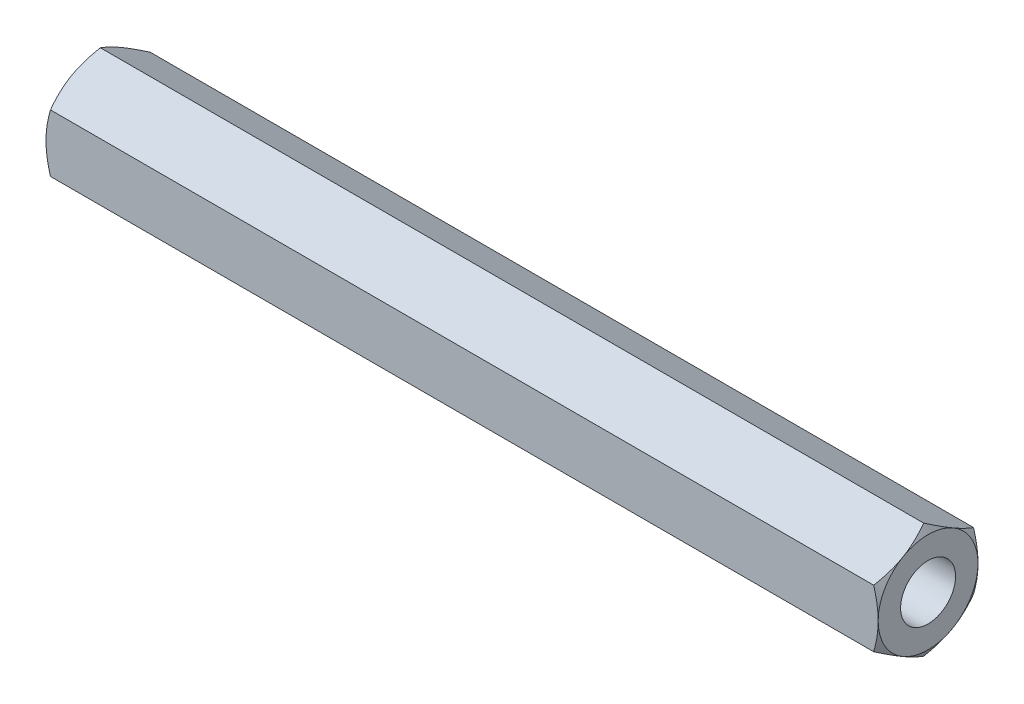
SolidWorks part; units mm, degrees
material "General Structural Steel"
ref_plane "Front Plane" through (0, 0, 0) normal (0, 0, 1) x (1, 0, 0)
ref_plane "Top Plane" through (0, 0, 0) normal (0, 1, 0) x (1, 0, 0)
ref_plane "Right Plane" through (0, 0, 0) normal (1, 0, 0) x (0, 0, -1)
sketch "Sketch1" plane through (0, 0, 0) normal (1, 0, 0) x (0, 0, -1)
  line L3 (0, -3.4641) -> (3, -1.7321)
  line L4 (3, -1.7321) -> (3, 1.7321)
  line L5 (3, 1.7321) -> (0, 3.4641)
  line L6 (0, 3.4641) -> (-3, 1.7321)
  line L7 (-3, 1.7321) -> (-3, -1.7321)
  line L8 (-3, -1.7321) -> (0, -3.4641)
  circle A0 centre (0, 0) radius 3 construction
  dimension "B" = 6
  dimension "C" = 6.9282
extrude "Boss-Extrude1" add sketch "Sketch1" along normal blind 50
sketch "Sketch2" plane through (0, 0, 0) normal (0, 0, 1) x (1, 0, 0)
  line L0 (0, 3.4641) -> (0.2679, 3.4641)
  line L1 (0, 0) -> (50, 0) construction
  line L2 (50, 1.7321) -> (50, -1.7321) construction
  line L3 (0, 3.4641) -> (0, 3)
  line L4 (50, 3.4641) -> (50, 1.7321) construction
  line L5 (50, 3.4641) -> (0, 3.4641) construction
  line L6 (50, 3.4641) -> (0, 3.4641) construction
  line L8 (0.2679, 3.4641) -> (0, 3)
  line L9 (49.7321, 3.4641) -> (50, 3)
  line L15 (50, 3.4641) -> (50, 3)
  line L16 (50, 3.4641) -> (49.7321, 3.4641)
  dimension "D1" = 30
revolve "Cut-Revolve1" cut sketch "Sketch2" angle 360 about L1
hole_wizard "Tapped Hole1" [suppressed] positions "Sketch4" profile "Sketch3" tap size "M3x0.5" standard "JIS"
sketch "Sketch4" [suppressed] plane through (0, 0, 0) normal (-1, 0, 0) x (0, 0, 1)
  point P0 (0, 0)
sketch "Sketch3" [suppressed] plane through (0, 0, 0) normal (0, 1, 0) x (0, 0, 1)
  line L0 (0, 9.2511) -> (0, 0)
  line L1 (0, 9.2511) -> (1.25, 8.5)
  line L2 (1.25, 8.5) -> (1.25, 0)
  line L3 (1.5, 0) -> (1.5, 8.5) construction
  line L5 (1.25, 0) -> (0, 0)
  line L10 (0, 9.2511) -> (-1.25, 8.5) construction
  line L11 (0, 0) -> (0, 9.2511) construction
  dimension "Tap Drill Dia." = 2.5
  dimension "Tap Drill Depth" = 8.5
  dimension "Drill Angle" = 118
  dimension "M" = 4
cosmetic thread "Hole Thread1" [suppressed] parameters "Mx2"=6, "M"=4
hole_wizard "Tapped Hole2" [suppressed] positions "Sketch6" profile "Sketch5" tap size "M3x0.5" standard "JIS"
sketch "Sketch6" [suppressed] plane through (24, 0, 0) normal (1, 0, 0) x (0, 0, -1)
  point P0 (0, 0)
sketch "Sketch5" [suppressed] plane through (24, 0, 0) normal (0, 1, 0) x (0, 0, -1)
  line L0 (0, 0) -> (0, 9.2511)
  line L1 (0, 9.2511) -> (1.25, 8.5)
  line L2 (1.25, 8.5) -> (1.25, 0)
  line L5 (1.25, 0) -> (0, 0)
  line L10 (0, 9.2511) -> (-1.25, 8.5) construction
  line L11 (0, 0) -> (0, 9.2511) construction
  dimension "Tap Drill Dia." = 2.5
  dimension "Tap Drill Depth" = 8.5
  dimension "Drill Angle" = 118
cosmetic thread "Hole Thread2" [suppressed] parameters "Mx2"=6, "M"=4
hole_wizard "Tapped Hole3" [suppressed] positions "Sketch8" profile "Sketch7" tap size "M3x0.5" standard "JIS"
sketch "Sketch8" [suppressed] plane through (0, 0, 0) normal (-1, 0, 0) x (0, 0, 1)
  point P0 (0, 0)
sketch "Sketch7" [suppressed] plane through (0, 0, 0) normal (0, 1, 0) x (0, 0, 1)
  line L0 (0, 0) -> (0, 10)
  line L1 (0, 10) -> (1.25, 10)
  line L2 (1.25, 10) -> (1.25, 0)
  line L5 (1.25, 0) -> (0, 0)
  line L11 (0, 0) -> (0, 10) construction
  dimension "Thru Tap Drill Dia." = 2.5
  dimension "Thru Tap Drill Depth" = 10
cosmetic thread "Hole Thread3" [suppressed] parameters "M"=4
sketch "Sketch21" plane through (0, 0, 0) normal (0, 0, 1) x (1, 0, 0)
  line L0 (0, 0) -> (50, 0)
  line L1 (0, 0) -> (50, 0) construction
  line L2 (0, 0) -> (0, 3)
  line L3 (0, 3) -> (50, 3)
  line L4 (50, 0) -> (50, 3)
revolve "Revolve1" add sketch "Sketch21" angle 360 about L1
hole_wizard "Tapped Hole4" positions "Sketch10" profile "Sketch9" tap size "M4x0.7" standard "JIS"
sketch "Sketch10" plane through (0, -0.1187, 0.0051) normal (1, 0, 0) x (0, 0, -1)
  point P0 (0.0051, 0.1187)
sketch "Sketch9" plane through (0, 0, 0) normal (0, 1, 0) x (0, 0, 1)
  line L0 (0, 0) -> (0, 12.4914)
  line L1 (0, 12.4914) -> (1.65, 11.5)
  line L2 (1.65, 11.5) -> (1.65, 0)
  line L3 (2, 0) -> (2, 11.5) construction
  line L5 (1.65, 0) -> (0, 0)
  line L10 (0, 12.4914) -> (-1.65, 11.5) construction
  line L11 (0, 0) -> (0, 12.4914) construction
  dimension "Tap Drill Dia." = 3.3
  dimension "Tap Drill Depth" = 11.5
  dimension "Drill Angle" = 118
  dimension "M" = 4
cosmetic thread "Hole Thread4" parameters "Mx2"=8, "M"=4
hole_wizard "Tapped Hole5" positions "Sketch12" profile "Sketch11" tap size "M4x0.7" standard "JIS"
sketch "Sketch12" plane through (50, 0.8438, 0.0751) normal (1, 0, 0) x (0, 0, -1)
  point P0 (0.0751, -0.8438)
sketch "Sketch11" plane through (50, 0, 0) normal (0, 1, 0) x (0, 0, -1)
  line L0 (0, 12.4914) -> (0, 0)
  line L1 (0, 12.4914) -> (1.65, 11.5)
  line L2 (1.65, 11.5) -> (1.65, 0)
  line L3 (2, 11.5) -> (2, 0) construction
  line L5 (1.65, 0) -> (0, 0)
  line L10 (0, 12.4914) -> (-1.65, 11.5) construction
  line L11 (0, 0) -> (0, 12.4914) construction
  dimension "Tap Drill Dia." = 3.3
  dimension "Tap Drill Depth" = 11.5
  dimension "Drill Angle" = 118
  dimension "N" = 4
cosmetic thread "Hole Thread5" parameters "Nx2"=8, "N"=4
sketch "Sketch13" plane through (0, 0, 0) normal (-1, 0, 0) x (0, 0, 1)
  circle A1 centre (0, 0) radius 1.65
  circle A3 centre (0, 0) radius 1.65
  dimension "D2" = 3.3
  dimension "D1" = 3.3
extrude "Boss-Extrude2" [suppressed] add sketch "Sketch13" against normal blind 8
sketch "Sketch14" plane through (50, 0, 0) normal (1, 0, 0) x (0, 0, -1)
  circle A1 centre (0, 0) radius 1.65
  circle A3 centre (0, 0) radius 1.65
  dimension "D2" = 3.3
  dimension "D1" = 3.3
extrude "Boss-Extrude3" [suppressed] add sketch "Sketch14" against normal blind 8
other "DeleteFace1" [suppressed]
hole_wizard "Tapped Hole6" [suppressed] positions "Sketch16" profile "Sketch15" tap size "M3x0.5" standard "JIS"
sketch "Sketch16" [suppressed] plane through (0, 105.4292, 93.8626) normal (-1, 0, 0) x (0, 0, 1)
  point P0 (-93.8626, -105.4292)
sketch "Sketch15" [suppressed] plane through (0, 0, 0) normal (0, 1, 0) x (0, 0, 1)
  line L0 (0, 0) -> (0, 12.2511)
  line L1 (0, 12.2511) -> (1.25, 11.5)
  line L2 (1.25, 11.5) -> (1.25, 0)
  line L5 (1.25, 0) -> (0, 0)
  line L10 (0, 12.2511) -> (-1.25, 11.5) construction
  line L11 (0, 0) -> (0, 12.2511) construction
  dimension "Tap Drill Dia." = 2.5
  dimension "Tap Drill Depth" = 11.5
  dimension "Drill Angle" = 118
cosmetic thread "Hole Thread6" [suppressed] parameters "Mx3"=7, "MD"=3
other "DeleteFace2" [suppressed]
hole_wizard "Tapped Hole7" [suppressed] positions "Sketch18" profile "Sketch17" tap size "M3x0.5" standard "JIS"
sketch "Sketch18" [suppressed] plane through (24, 0.4538, -5.059) normal (1, 0, 0) x (0, 0, -1)
  point P0 (-5.059, -0.4538)
sketch "Sketch17" [suppressed] plane through (24, 0, 0) normal (0, 1, 0) x (0, 0, -1)
  line L0 (0, 0) -> (0, 12.2511)
  line L1 (0, 12.2511) -> (1.25, 11.5)
  line L2 (1.25, 11.5) -> (1.25, 0)
  line L5 (1.25, 0) -> (0, 0)
  line L10 (0, 12.2511) -> (-1.25, 11.5) construction
  line L11 (0, 0) -> (0, 12.2511) construction
  dimension "Tap Drill Depth" = 11.5
  dimension "Drill Angle" = 118
  dimension "Tap Drill Dia." = 2.5
cosmetic thread "Hole Thread7" [suppressed] parameters "Nx3"=9, "ND"=3
equation "\"D1@Sketch14\"=\"Tap Drill Dia.@Sketch11\""
equation "\"D2@Sketch14\"=\"Tap Drill Dia.@Sketch9\""
equation "\"D1@Sketch13\"=\"Tap Drill Dia.@Sketch9\""
equation "\"D2@Sketch13\"=\"Tap Drill Dia.@Sketch11\""
equation "\"D1@Sketch20\"= \"Tap Drill Dia.@Sketch17\""
equation "\"D2@Sketch20\"= \"Tap Drill Dia.@Sketch9\""
equation "\"D1@Boss-Extrude2\" = \"M\" * 2"
equation "\"D1@Boss-Extrude3\" = \"N\" * 2"
equation "\"M\"=4"
equation "\"N\"=4"
equation "\"Mx3\"= \"M\" * 3"
equation "\"Nx3\"= \"N\" * 3"
